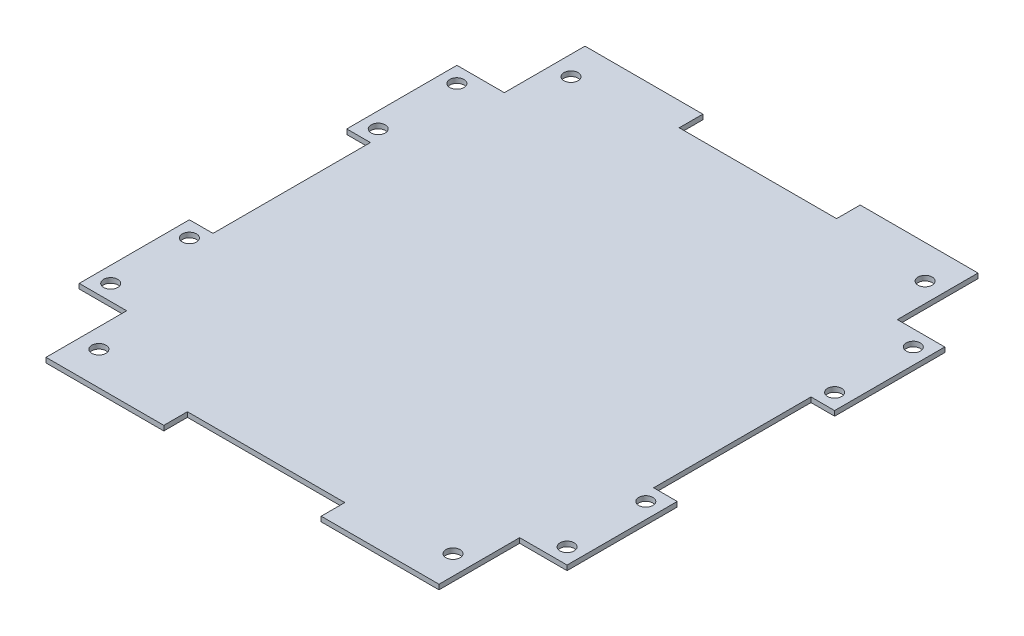
SolidWorks part; units mm, degrees
ref_plane "Front Plane" through (0, 0, 0) normal (0, 0, 1) x (1, 0, 0)
ref_plane "Top Plane" through (0, 0, 0) normal (0, 1, 0) x (1, 0, 0)
ref_plane "Right Plane" through (0, 0, 0) normal (1, 0, 0) x (0, 0, -1)
sketch "Sketch1" plane through (0, 0, 0) normal (0, 1, 0) x (1, 0, 0)
  line L0 (-25.4, 86.995) -> (-63.4314, 86.995)
  line L1 (-88.9, -101.6) -> (88.9, -101.6) construction
  line L2 (101.6, -88.9) -> (101.6, 88.9) construction
  line L3 (88.9, 101.6) -> (-88.9, 101.6) construction
  line L4 (-78.74, -60.96) -> (-63.4314, -60.96)
  line L5 (-63.4314, -60.96) -> (-63.4314, -86.995)
  line L6 (-63.4314, -86.995) -> (-25.4, -86.995)
  line L7 (63.4314, -86.995) -> (63.4314, -60.96)
  line L8 (63.4314, -60.96) -> (78.74, -60.96)
  line L9 (78.74, -60.96) -> (78.74, -25.4)
  line L10 (78.74, 60.96) -> (63.4314, 60.96)
  line L11 (63.4314, 60.96) -> (63.4314, 86.995)
  line L12 (63.4314, 86.995) -> (25.4, 86.995)
  line L13 (-63.4314, 86.995) -> (-63.4314, 60.96)
  line L14 (-63.4314, 60.96) -> (-78.74, 60.96)
  line L15 (-78.74, 60.96) -> (-78.74, 25.4)
  line L16 (-78.74, -25.4) -> (-78.74, -60.96)
  line L17 (-78.74, -25.4) -> (-71.12, -25.4)
  line L19 (-78.74, 25.4) -> (-71.12, 25.4)
  line L20 (-71.12, -25.4) -> (-71.12, 25.4)
  line L22 (-25.4, 86.995) -> (-25.4, 79.375)
  line L23 (-25.4, 79.375) -> (25.4, 79.375)
  line L24 (25.4, 86.995) -> (25.4, 79.375)
  line L25 (78.74, 25.4) -> (71.12, 25.4)
  line L27 (78.74, -25.4) -> (71.12, -25.4)
  line L28 (71.12, 25.4) -> (71.12, -25.4)
  line L30 (25.4, -86.995) -> (25.4, -79.375)
  line L31 (25.4, -79.375) -> (-25.4, -79.375)
  line L32 (-25.4, -86.995) -> (-25.4, -79.375)
  line L33 (78.74, 25.4) -> (78.74, 60.96)
  line L34 (25.4, -86.995) -> (63.4314, -86.995)
  line L35 (-101.6, 88.9) -> (-101.6, -88.9) construction
  arc A0 (88.9, -101.6) -> (101.6, -88.9) centre (88.9, -88.9) ccw construction
  arc A1 (-101.6, -88.9) -> (-88.9, -101.6) centre (-88.9, -88.9) ccw construction
  arc A2 (101.6, 88.9) -> (88.9, 101.6) centre (88.9, 88.9) ccw construction
  arc A3 (-101.6, 88.9) -> (-88.9, 101.6) centre (-88.9, 88.9) cw construction
  circle A4 centre (-57.15, 76.2) radius 2.286
  circle A5 centre (57.15, 76.2) radius 2.286
  circle A6 centre (57.15, -76.2) radius 2.286
  circle A7 centre (-57.15, -76.2) radius 2.286
  point P3 (0, 101.6)
  point P5 (101.6, 0)
  point P13 (101.6, 101.6)
  point P16 (-101.6, 101.6)
  point P38 (-71.12, 0)
  point P55 (0, -79.375)
  point P56 (0, 79.375)
  point P57 (71.12, 0)
  dimension "D2" = 12.7
  dimension "D11" = 4.572
  dimension "D8" = 44.45
  dimension "D1" = 203.2
  dimension "D3" = 203.2
  dimension "D4" = 22.86
  dimension "D5" = 15.3086
  dimension "D6" = 35.56
  dimension "D7" = 173.99
  dimension "D12" = 50.8
  dimension "D13" = 25.4
  dimension "D14" = 44.45
  dimension "D15" = 25.4
  dimension "D18" = 7.62
extrude "Boss-Extrude1" add sketch "Sketch1" along normal blind 1.5875
sketch "Sketch2" plane through (0, 1.5875, 0) normal (0, 1, 0) x (1, 0, 0)
  line L0 (0, -1000) -> (0, 49000) construction
  line L1 (-1000, 0) -> (49000, 0) construction
  line L2 (-78.74, -60.96) -> (-63.4314, -60.96) construction
  line L3 (-71.12, -25.4) -> (-78.74, -25.4) construction
  line L4 (-78.74, -25.4) -> (-78.74, -60.96) construction
  circle A0 centre (-73.66, -30.48) radius 2.286
  circle A1 centre (-73.66, -55.88) radius 2.286
  circle A2 centre (73.66, -55.88) radius 2.286
  circle A3 centre (73.66, -30.48) radius 2.286
  circle A4 centre (73.66, 30.48) radius 2.286
  circle A5 centre (73.66, 55.88) radius 2.286
  circle A6 centre (-73.66, 55.88) radius 2.286
  circle A7 centre (-73.66, 30.48) radius 2.286
  dimension "D1" = 4.572
  dimension "D2" = 5.08
  dimension "D3" = 5.08
  dimension "D4" = 5.08
extrude "Cut-Extrude1" cut sketch "Sketch2" against normal through all
